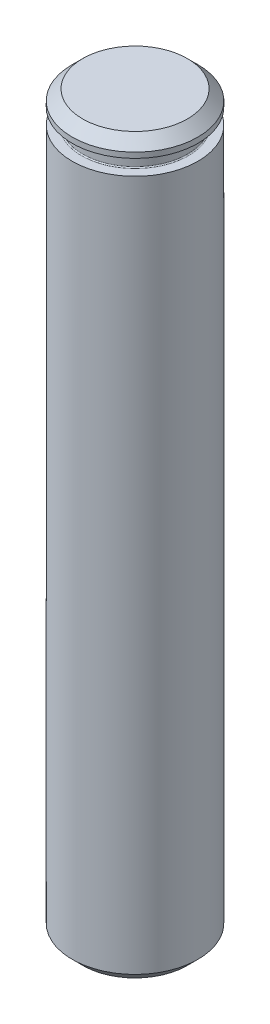
SolidWorks part; units mm, degrees
material "1060 Alloy"
ref_plane "Front Plane" through (0, 0, 0) normal (0, 0, 1) x (1, 0, 0)
ref_plane "Top Plane" through (0, 0, 0) normal (0, 1, 0) x (1, 0, 0)
ref_plane "Right Plane" through (0, 0, 0) normal (1, 0, 0) x (0, 0, -1)
sketch "Sketch1" plane through (0, 0, 0) normal (0, 0, 1) x (1, 0, 0)
  line L0 (0, 0) -> (0, 32.419) construction
  line L2 (0, 0) -> (3, 0)
  line L3 (0, 0) -> (0, 35)
  line L4 (0, 35) -> (3, 35)
  line L5 (3, 0) -> (3, 35)
  dimension "D1" = 6
  dimension "D2" = 35
revolve "Revolve1" add sketch "Sketch1" angle 360 about L0
ref_plane "Plane1" through (0, 0, 0) normal (-1, 0, 0) x (0, 0, -1)
sketch "Sketch3" plane through (0, 0, 0) normal (-1, 0, 0) x (0, 0, -1)
  line L0 (2.55, -34.24) -> (3.6, -34.24)
  line L1 (3.6, -34.24) -> (3.6, -33.5)
  line L2 (3.6, -33.5) -> (2.55, -33.5)
  line L3 (2.5, -33.55) -> (2.5, -34.19)
  line L4 (0, -50) -> (0, 50) construction
  line L6 (-3, -35) -> (3, -35) construction
  arc A0 (2.5, -34.19) -> (2.55, -34.24) centre (2.55, -34.19) ccw
  arc A1 (2.5, -33.55) -> (2.55, -33.5) centre (2.55, -33.55) cw
  dimension "D1" = 0.05
  dimension "D2" = 0.05
  dimension "D3" = 1.5
  dimension "D4" = 2.5
  dimension "D5" = 0.74
revolve "Groove for DIN 471 - 4 x 0.4, Circlip for shafts - normal1" cut sketch "Sketch3"
chamfer "Chamfer1" distance 0.5 angle 45 2 edges at (0, 35, -3) (0, 0, -3)
